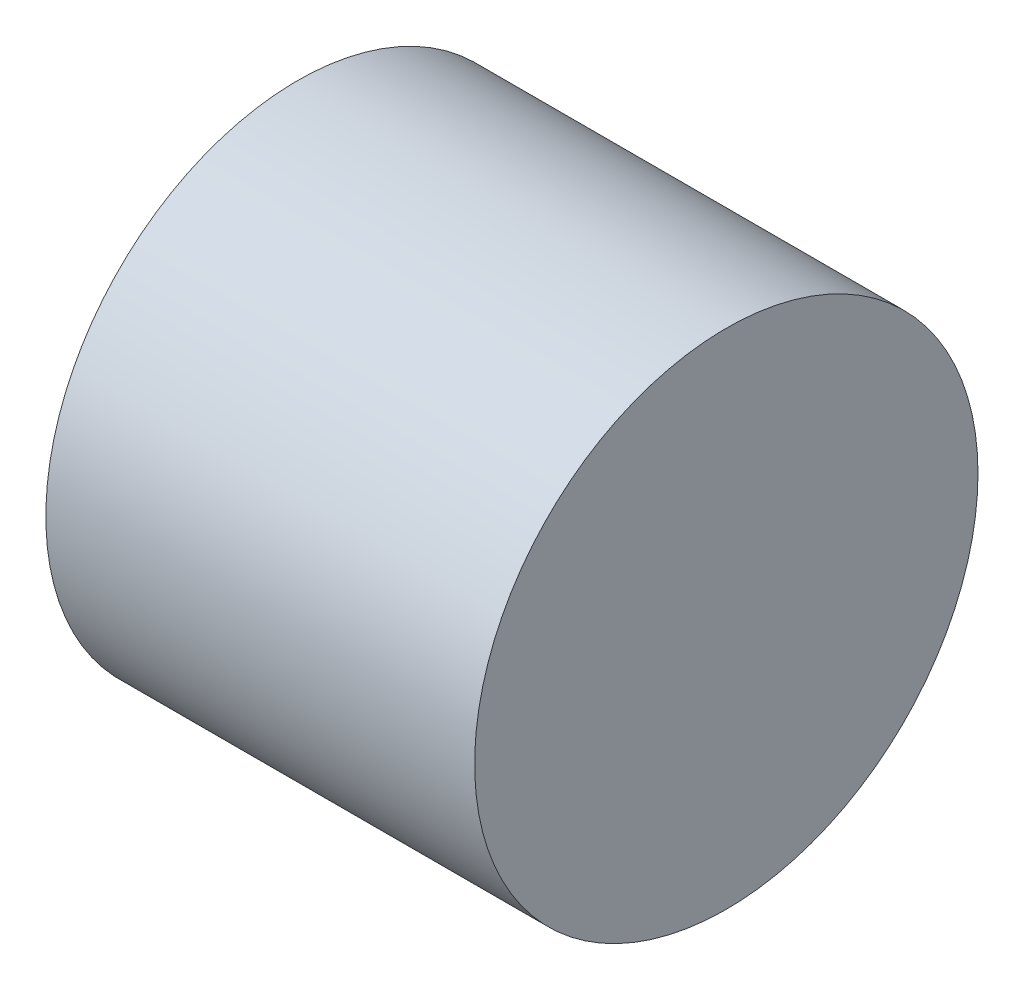
SolidWorks part; units mm, degrees
ref_plane "Front Plane" through (0, 0, 0) normal (0, 0, 1) x (1, 0, 0)
ref_plane "Top Plane" through (0, 0, 0) normal (0, 1, 0) x (1, 0, 0)
ref_plane "Right Plane" through (0, 0, 0) normal (1, 0, 0) x (0, 0, -1)
sketch "Sketch1" plane through (0, 0, 0) normal (1, 0, 0) x (0, 0, -1)
  circle A0 centre (0, 0) radius 27
extrude "Boss-Extrude1" add sketch "Sketch1" along normal blind 46
